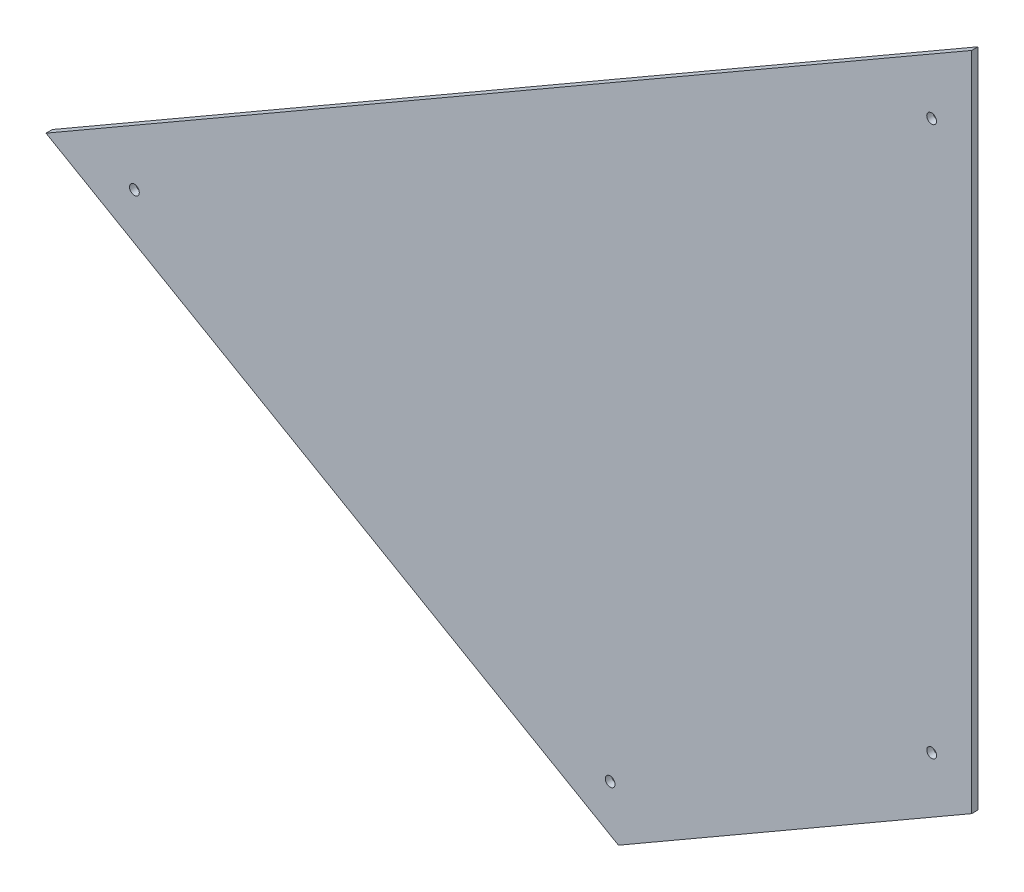
SolidWorks part; units mm, degrees
material "Акрил (Средняя-высокая ударопрочность)"
ref_plane "Спереди" through (0, 0, 0) normal (0, 0, 1) x (1, 0, 0)
ref_plane "Сверху" through (0, 0, 0) normal (0, 1, 0) x (1, 0, 0)
ref_plane "Справа" through (0, 0, 0) normal (1, 0, 0) x (0, 0, -1)
sketch "Эскиз1" plane through (0, 0, 0) normal (0, 0, 1) x (1, 0, 0)
  line L0 (0, 0) -> (-293.1432, -169.2612)
  line L1 (-293.1432, -169.2612) -> (-111.861, -273.9061)
  line L2 (-111.861, -273.9061) -> (0, -209.3174)
  line L3 (0, -209.3174) -> (0, 0)
  dimension "D1" = 338.5
  dimension "D2" = 209.3174
  dimension "D3" = 129.1688
  dimension "D4" = 209.3174
extrude "Бобышка-Вытянуть1" add sketch "Эскиз1" along normal blind 2
sketch "Эскиз3" plane through (0, 0, 0) normal (0, 0, -1) x (-1, 0, 0)
  circle A0 centre (12.6827, -25.0018) radius 1.55
  circle A1 centre (12.6827, -198.9616) radius 1.55
  circle A2 centre (114.4893, -257.7448) radius 1.55
  circle A3 centre (265.1494, -170.7764) radius 1.55
extrude "Вырез-Вытянуть1" cut sketch "Эскиз3" against normal blind 2
